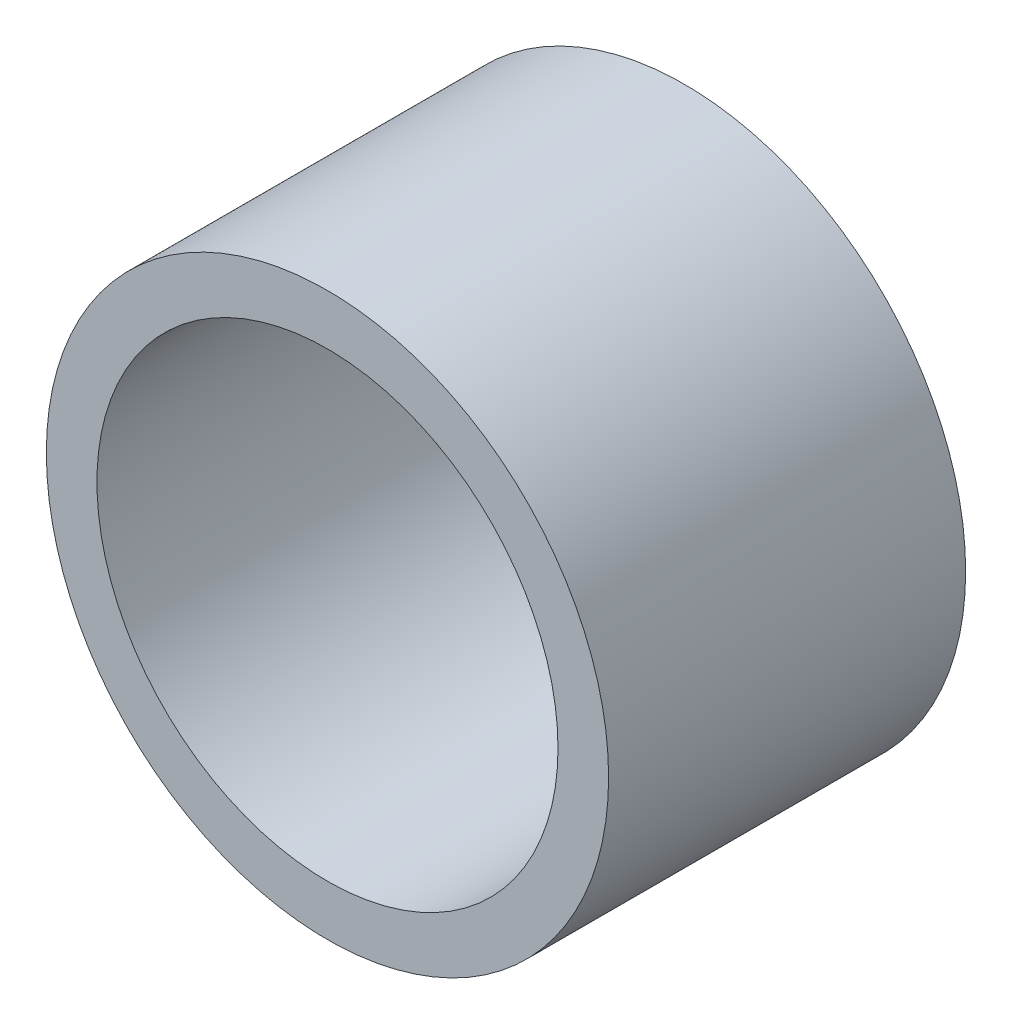
SolidWorks part; units mm, degrees
ref_plane "Front Plane" through (0, 0, 0) normal (0, 0, 1) x (1, 0, 0)
ref_plane "Top Plane" through (0, 0, 0) normal (0, 1, 0) x (1, 0, 0)
ref_plane "Right Plane" through (0, 0, 0) normal (1, 0, 0) x (0, 0, -1)
sketch "Sketch1" plane through (0, 0, 0) normal (0, 0, 1) x (1, 0, 0)
  circle A0 centre (0, 0) radius 5
  dimension "D1" = 10
extrude "Boss-Extrude1" add sketch "Sketch1" along normal blind 6.35
sketch "Sketch2" plane through (0, 0, 6.35) normal (0, 0, 1) x (1, 0, 0)
  circle A0 centre (0, 0) radius 4.1
extrude "Cut-Extrude1" cut sketch "Sketch2" against normal through all
